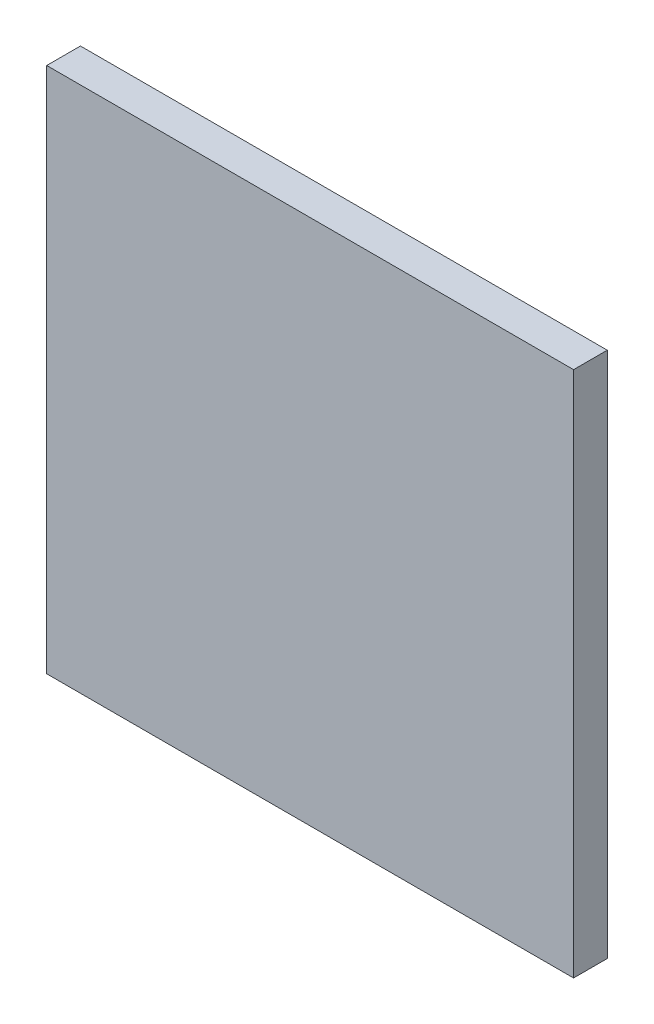
SolidWorks part; units mm, degrees
ref_plane "Front Plane" through (0, 0, 0) normal (1, 0, 0) x (0, 1, 0)
ref_plane "Top Plane" through (0, 0, 0) normal (0, 0, 1) x (0, 1, 0)
ref_plane "Right Plane" through (0, 0, 0) normal (0, 1, 0) x (-1, 0, 0)
sketch "Sketch1" plane through (0, 0, 0) normal (0, 0, 1) x (0, 1, 0)
  line L1 (-25, 25) -> (25, 25)
  line L2 (-25, 25) -> (-25, -25)
  line L3 (-25, -25) -> (25, -25)
  line L4 (25, 25) -> (25, -25)
  line L5 (-25, 25) -> (25, -25) construction
  line L6 (-25, -25) -> (25, 25) construction
  point P0 (0, 0)
  dimension "D1" = 50
  dimension "D2" = 50
extrude "Boss-Extrude1" add sketch "Sketch1" along normal blind 3.2
